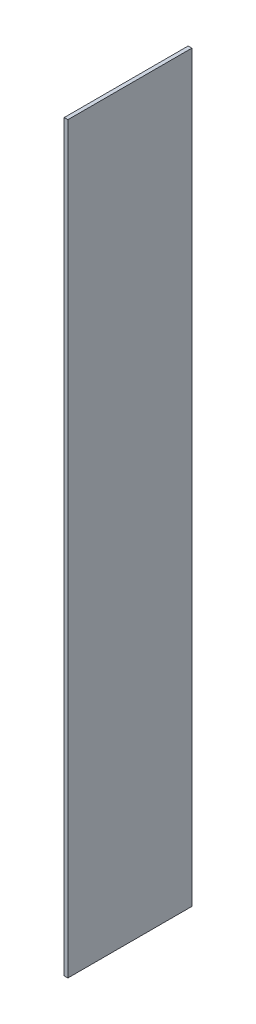
SolidWorks part; units mm, degrees
ref_plane "Front Plane" through (0, 0, 0) normal (0, 0, 1) x (1, 0, 0)
ref_plane "Top Plane" through (0, 0, 0) normal (0, 1, 0) x (1, 0, 0)
ref_plane "Right Plane" through (0, 0, 0) normal (1, 0, 0) x (0, 0, -1)
sketch "Sketch1" plane through (0, 0, 0) normal (0, 1, 0) x (1, 0, 0)
  line L1 (-0.75, 25) -> (0.75, 25)
  line L2 (-0.75, 25) -> (-0.75, -25)
  line L3 (-0.75, -25) -> (0.75, -25)
  line L4 (0.75, 25) -> (0.75, -25)
  line L5 (-0.75, 25) -> (0.75, -25) construction
  line L6 (-0.75, -25) -> (0.75, 25) construction
  point P0 (0, 0)
  dimension "D1" = 50
  dimension "D2" = 1.5
extrude "Boss-Extrude1" add sketch "Sketch1" along normal mid plane 300
